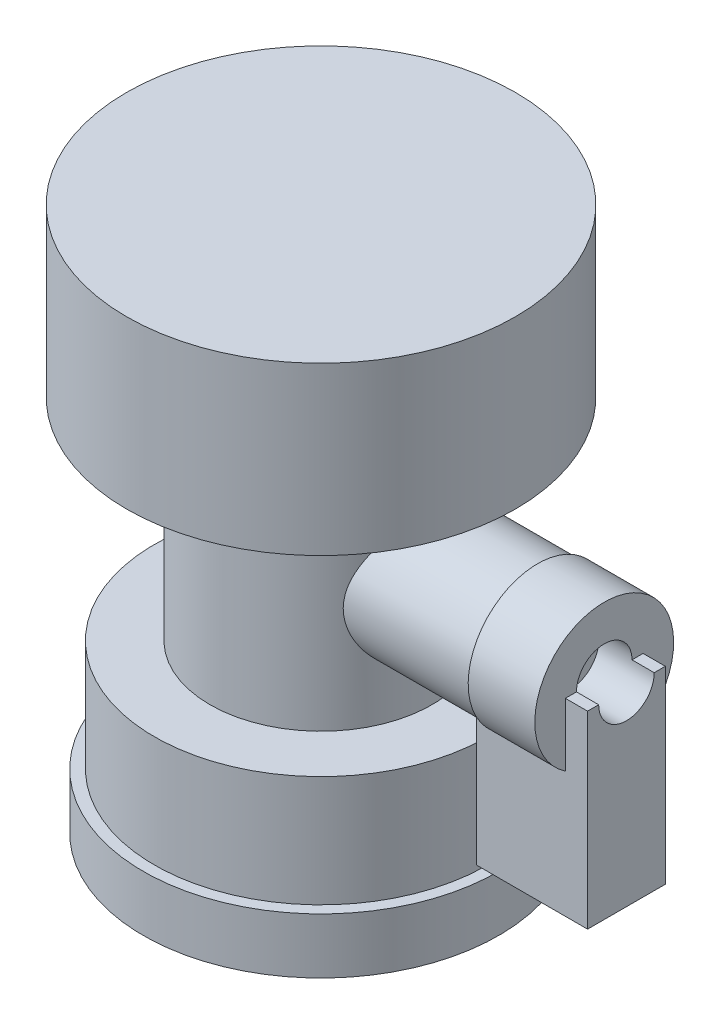
SolidWorks part; units mm, degrees
ref_plane "Front" through (0, 0, 0) normal (0, 0, 1) x (1, 0, 0)
ref_plane "Top" through (0, 0, 0) normal (0, 1, 0) x (1, 0, 0)
ref_plane "Right" through (0, 0, 0) normal (1, 0, 0) x (0, 0, -1)
sketch "Sketch1" plane through (0, 0, 0) normal (0, 1, 0) x (1, 0, 0)
  circle A0 centre (0, 0) radius 10
  dimension "D1" = 20
extrude "Boss-Extrude1" add sketch "Sketch1" along normal blind 19
sketch "Sketch2" plane through (0, 0, 0) normal (1, 0, 0) x (0, 0, -1)
  line L0 (0, 0) -> (0, 19) construction
  line L2 (14.2454, 9.5) -> (-16.7208, 9.5) construction
  circle A0 centre (0, 9.5) radius 6
  dimension "D1" = 12
  dimension "D2" = 9.5
  dimension "D3" = 0
extrude "Boss-Extrude2" add sketch "Sketch2" along normal blind 19.5
sketch "Sketch7" plane through (0, 0, 0) normal (0, -1, 0) x (1, 0, 0)
  circle A0 centre (0, 0) radius 15
  dimension "D1" = 30
extrude "Boss-Extrude9" add sketch "Sketch7" along normal blind 10
sketch "Sketch9" plane through (0, -10, 0) normal (0, -1, 0) x (1, 0, 0)
  circle A0 centre (0, 0) radius 16
  dimension "D1" = 32
extrude "Boss-Extrude10" add sketch "Sketch9" along normal blind 5
sketch "Sketch10" plane through (0, 19, 0) normal (0, 1, 0) x (1, 0, 0)
  circle A0 centre (0, 0) radius 17.5
  dimension "D1" = 35
extrude "Boss-Extrude11" add sketch "Sketch10" along normal blind 15
sketch "Sketch11" plane through (19.5, 0, 0) normal (1, 0, 0) x (0, 0, -1)
  circle A0 centre (0, 9.5) radius 6.25
  dimension "D1" = 12.5
extrude "Boss-Extrude12" add sketch "Sketch11" along normal blind 6
sketch "Sketch12" plane through (0, 0, 0) normal (0, 1, 0) x (1, 0, 0)
  line L0 (0, 0) -> (43.9547, 0) construction
  line L1 (22.5, -10.7528) -> (22.5, 13.4013) construction
  line L3 (25.5, -6.25) -> (25.5, 6.25) construction
  line L5 (17.5, 3.5) -> (27.5, 3.5)
  line L6 (17.5, 3.5) -> (17.5, -3.5)
  line L7 (17.5, -3.5) -> (27.5, -3.5)
  line L8 (27.5, 3.5) -> (27.5, -3.5)
  line L9 (17.5, 3.5) -> (27.5, -3.5) construction
  line L10 (17.5, -3.5) -> (27.5, 3.5) construction
  point P5 (22.5, 0)
  dimension "D1" = 3
  dimension "D2" = 10
  dimension "D3" = 7
extrude "Boss-Extrude13" add sketch "Sketch12" along normal blind 10 and the other way blind 7
sketch "Sketch13" plane through (25.5, 0, 0) normal (1, 0, 0) x (0, 0, -1)
  line L0 (3.5, 10) -> (-3.5, 10) construction
  circle A0 centre (0, 10) radius 2.5
  dimension "D1" = 5
extrude "Cut-Extrude1" cut sketch "Sketch13" against normal blind 3 and the other way up to next
